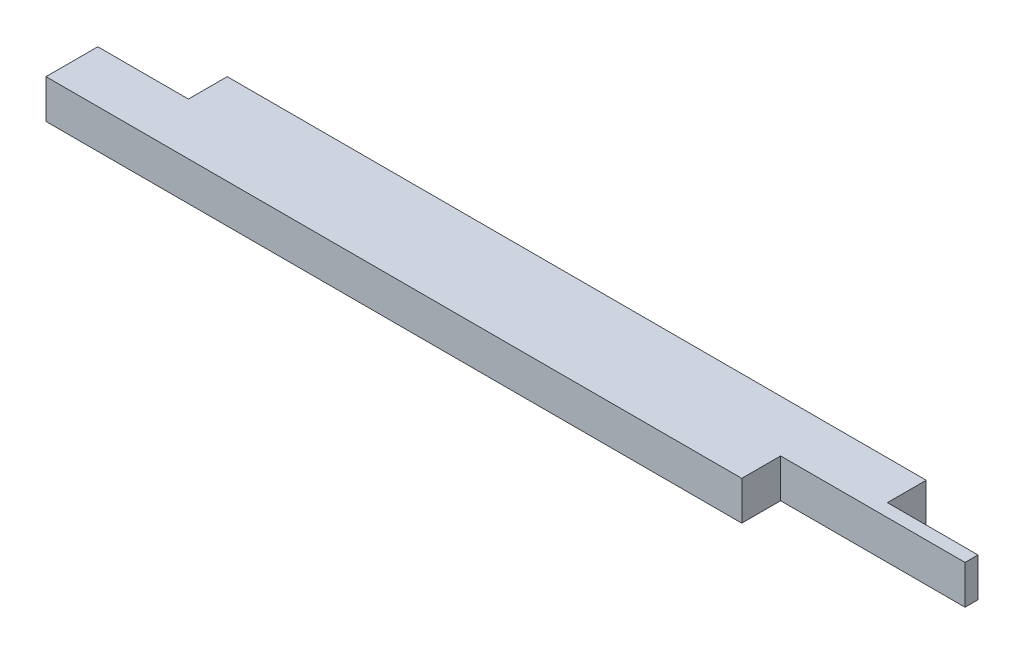
SolidWorks part; units mm, degrees
material "Pine"
ref_plane "Front Plane" through (0, 0, 0) normal (0, 0, 1) x (1, 0, 0)
ref_plane "Top Plane" through (0, 0, 0) normal (0, 1, 0) x (1, 0, 0)
ref_plane "Right Plane" through (0, 0, 0) normal (1, 0, 0) x (0, 0, -1)
sketch "Sketch1" plane through (0, 0, 0) normal (0, 1, 0) x (1, 0, 0)
  line L1 (0, 0) -> (863.6, 0)
  line L2 (0, 0) -> (0, 88.9)
  line L3 (0, 88.9) -> (863.6, 88.9)
  line L4 (863.6, 0) -> (863.6, 88.9)
  dimension "D1" = 88.9
  dimension "D2" = 863.6
extrude "Boss-Extrude1" add sketch "Sketch1" along normal blind 38.1
sketch "Sketch3" plane through (0, 38.1, 0) normal (0, 1, 0) x (1, 0, 0)
  line L1 (0, 88.9) -> (88.9, 88.9)
  line L2 (0, 88.9) -> (0, 50.8)
  line L3 (0, 50.8) -> (88.9, 50.8)
  line L4 (88.9, 88.9) -> (88.9, 50.8)
  line L5 (863.6, 88.9) -> (774.7, 88.9)
  line L6 (863.6, 88.9) -> (863.6, 50.8)
  line L7 (863.6, 50.8) -> (774.7, 50.8)
  line L8 (774.7, 88.9) -> (774.7, 50.8)
  dimension "D1" = 88.9
  dimension "D2" = 88.9
  dimension "D3" = 38.1
  dimension "D4" = 38.1
extrude "Cut-Extrude1" cut sketch "Sketch3" against normal through all
sketch "Sketch4" plane through (0, 38.1, 0) normal (0, 1, 0) x (1, 0, 0)
  line L1 (863.6, 0) -> (682.625, 0)
  line L2 (863.6, 0) -> (863.6, 38.1)
  line L3 (863.6, 38.1) -> (682.625, 38.1)
  line L4 (682.625, 0) -> (682.625, 38.1)
  point P5 (682.625, 19.05)
  dimension "D1" = 180.975
  dimension "D2" = 38.1
extrude "Cut-Extrude2" cut sketch "Sketch4" against normal through all
